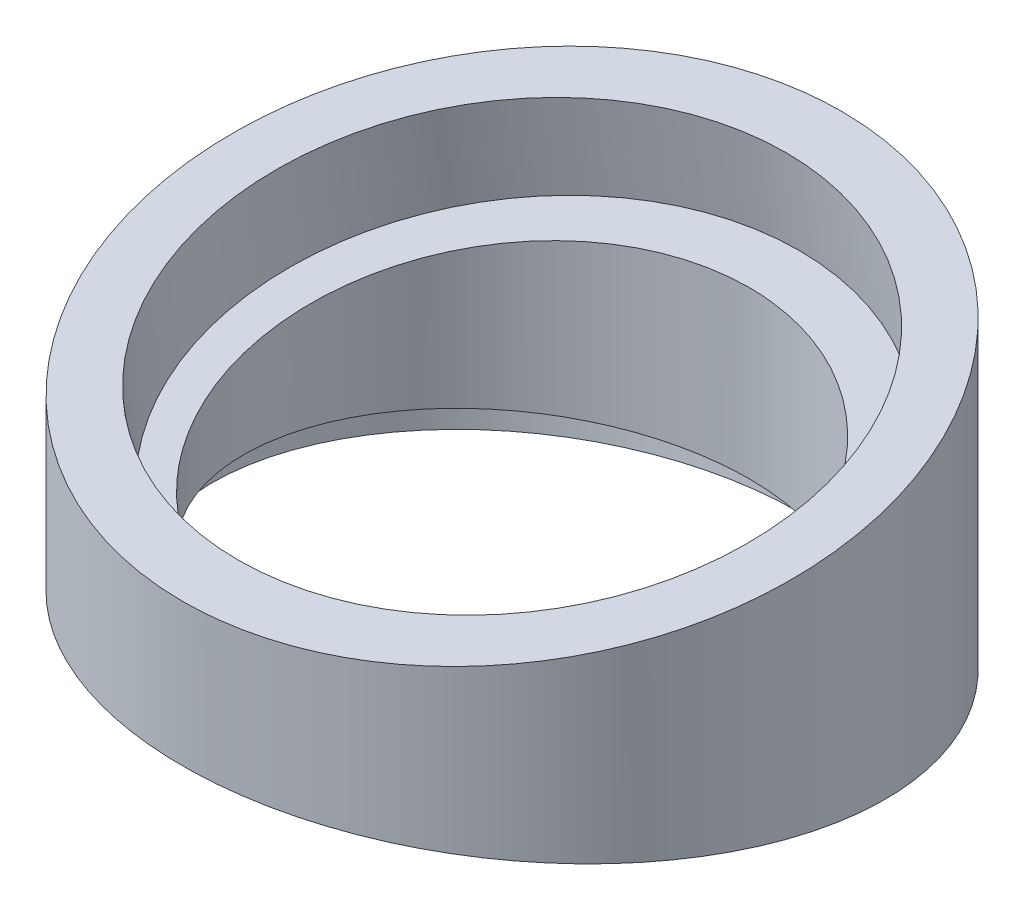
SolidWorks part; units mm, degrees
ref_plane "前视基准面" through (0, 0, 0) normal (0, 0, 1) x (1, 0, 0)
ref_plane "上视基准面" through (0, 0, 0) normal (0, 1, 0) x (1, 0, 0)
ref_plane "右视基准面" through (0, 0, 0) normal (1, 0, 0) x (0, 0, -1)
sketch "草图1" plane through (0, 0, 0) normal (0, 1, 0) x (1, 0, 0)
  circle A0 centre (0, 0) radius 25
  dimension "D1" = 50
extrude "凸台-拉伸1" add sketch "草图1" along normal blind 30
sketch "草图3" plane through (0, 0, 0) normal (1, 0, 0) x (0, 0, -1)
  line L0 (-25, 18) -> (25, 25.1889)
  line L1 (-25, 30) -> (-25, 0) construction
  line L2 (25, 0) -> (25, 30) construction
  line L3 (25, 25.1889) -> (25, 39.51)
  line L4 (25, 39.51) -> (-25, 39.51)
  line L5 (-25, 39.51) -> (-25, 18)
  line L6 (-25, 0) -> (25, 0) construction
  line L7 (0, 0) -> (0, 39.51) construction
  line L8 (-21.6213, 11.4138) -> (19.9512, 17.391) construction
  line L9 (-21.6213, 11.4138) -> (-23.6137, 25.2713) construction
  line L10 (19.9512, 17.391) -> (17.9588, 31.2485) construction
  line L11 (-23.6137, 25.2713) -> (17.9588, 31.2485) construction
  line L12 (-21.6213, 11.4138) -> (17.9588, 31.2485) construction
  line L13 (19.9512, 17.391) -> (-23.6137, 25.2713) construction
  line L14 (25, 0) -> (-25, 7.1889)
  line L19 (-25, 7.1889) -> (-25, -17.3585)
  line L20 (-25, -17.3585) -> (25, -17.3585)
  line L21 (25, -17.3585) -> (25, 0)
  line L22 (20.7863, 0.6058) -> (-20.7863, 6.5831) construction
  line L23 (20.7863, 0.6058) -> (21.142, 3.0804) construction
  line L24 (-20.7863, 6.5831) -> (-20.4305, 9.0576) construction
  line L25 (21.142, 3.0804) -> (-20.4305, 9.0576) construction
  point P14 (-1.8313, 21.3312)
  point P22 (0, 3.5944)
  dimension "D1" = 8.182
  dimension "D2" = 8.182
  dimension "D3" = 7
  dimension "D4" = 0
  dimension "D5" = 42
  dimension "D6" = 2.5
  dimension "D7" = 21
  dimension "D8" = 14
  dimension "D9" = 42
  dimension "D10" = 18
extrude "切除-拉伸1" cut sketch "草图3" against normal mid plane 63
sketch "草图7" plane through (0, 21.1571, 3.0419) normal (0, 0.9898, 0.1423) x (1, 0, 0)
  circle A0 centre (0, 3.0732) radius 21
  ellipse E0 centre (0, 3.0732) end of major axis (0, -22.1839) minor radius 25 construction
  dimension "D1" = 42
extrude "切除-拉伸2" cut sketch "草图7" against normal blind 7
sketch "草图8" plane through (0, 3.5216, -0.5063) normal (0, -0.9898, 0.1423) x (-1, 0, 0)
  line L0 (25, -0.5115) -> (-25, -0.5115) construction
  circle A0 centre (0, 0.4885) radius 21
  dimension "D1" = 42
  dimension "D2" = 1
extrude "切除-拉伸3" cut sketch "草图8" against normal blind 3.5
sketch "草图9" plane through (0, 0, 0) normal (0, 1, 0) x (1, 0, 0)
  circle A0 centre (0, 0) radius 18
  dimension "D1" = 36
extrude "切除-拉伸4" cut sketch "草图9" along normal blind 107.5
